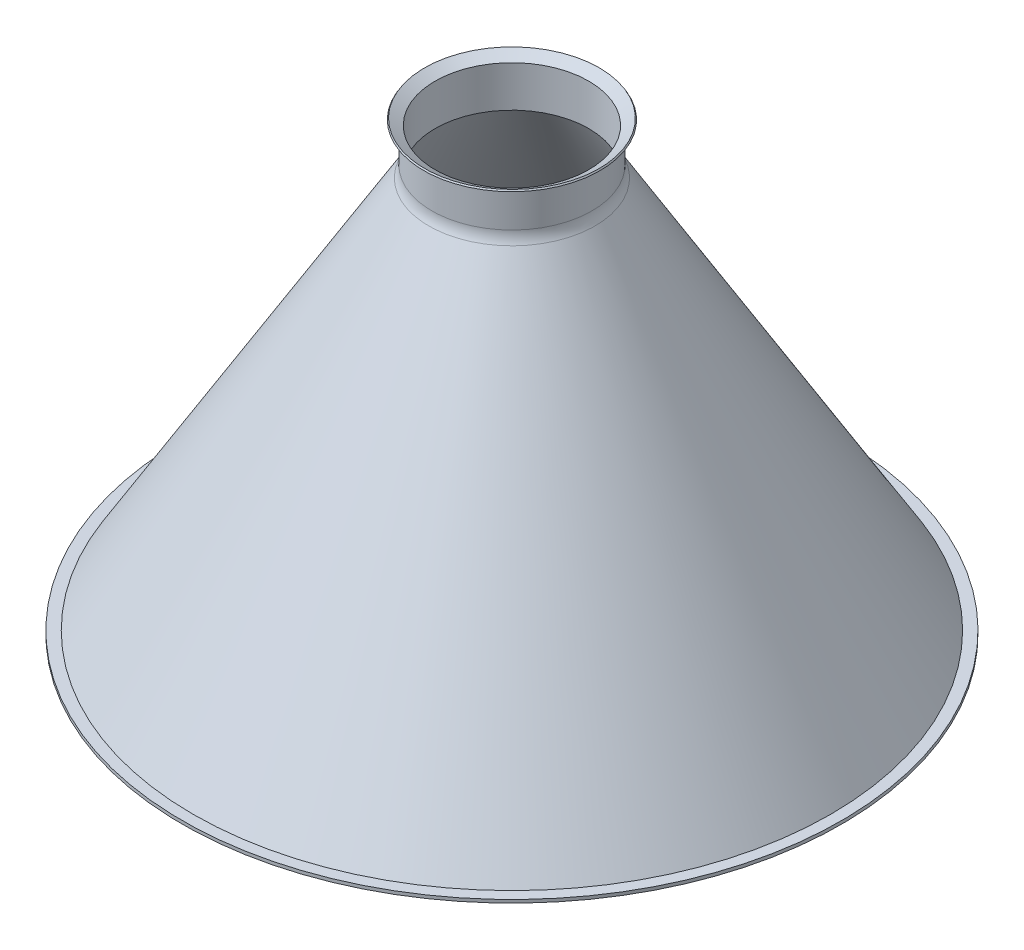
SolidWorks part; units mm, degrees
ref_plane "Front Plane" through (0, 0, 0) normal (0, 0, 1) x (1, 0, 0)
ref_plane "Top Plane" through (0, 0, 0) normal (0, 1, 0) x (1, 0, 0)
ref_plane "Right Plane" through (0, 0, 0) normal (1, 0, 0) x (0, 0, -1)
sketch "Sketch1" plane through (0, 0, 0) normal (0, 0, 1) x (1, 0, 0)
  line L0 (0, 0) -> (0, 71.8908) construction
  line L1 (25.2615, 74.5395) -> (25.2615, 61.8395)
  line L2 (25.2615, 61.8395) -> (100.6281, -63.5436)
  line L3 (24.2615, 74.5395) -> (24.2615, 61.5621)
  line L4 (24.2615, 61.5621) -> (100.0624, -64.5436)
  line L5 (100.0624, -64.5436) -> (104.0624, -64.5436)
  line L7 (25.2615, 74.5395) -> (27.8328, 76.085)
  line L8 (27.8328, 76.085) -> (27.5673, 76.5266)
  line L9 (27.5673, 76.5266) -> (24.2615, 74.5395)
  line L10 (104.0624, -64.5436) -> (104.0624, -63.5436)
  line L11 (104.0624, -63.5436) -> (100.6281, -63.5436)
  line L12 (25.2615, 61.8395) -> (100.9195, -64.0284) construction
  dimension "D1" = 25.4
  dimension "D2" = 1
  dimension "D3" = 4
  dimension "D5" = 12.7
  dimension "D6" = 3
  dimension "D4" = 1
revolve "Revolve1" add sketch "Sketch1" angle 360 about L0
fillet "Fillet1" radius 7 1 edges at (0, 61.8395, -25.2615)
